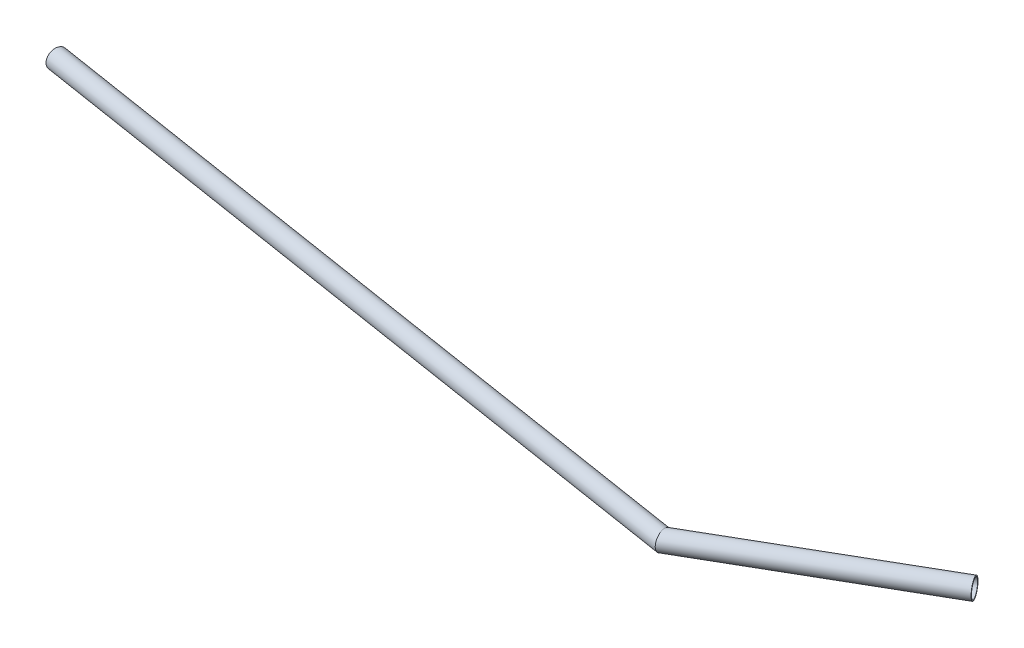
SolidWorks part; units mm, degrees
ref_plane "Front Plane" through (0, 0, 0) normal (0, 0, 1) x (1, 0, 0)
ref_plane "Top Plane" through (0, 0, 0) normal (0, 1, 0) x (1, 0, 0)
ref_plane "Right Plane" through (0, 0, 0) normal (1, 0, 0) x (0, 0, -1)
sketch "Sketch1" plane through (0, 0, 0) normal (0, 1, 0) x (1, 0, 0)
  line L0 (-465, 0) -> (465, 0) construction
  line L1 (465, 0) -> (265, -115.4701)
  line L2 (-465, 0) -> (265, -115.4701)
  point P3 (0, 0)
  dimension "D1" = 930
  dimension "D2" = 30
  dimension "D3" = 200
ref_plane "Plane1" through (-465, 0, 0) normal (0.9877, 0, 0.1562) x (0.1562, 0, -0.9877)
sketch "Sketch2" plane through (-465, 0, 0) normal (0.9877, 0, 0.1562) x (0.1562, 0, -0.9877)
  line L0 (0, 0) -> (145.2992, 0) construction
  line L1 (145.2992, 0) -> (0, 0) construction
  circle A0 centre (0, 0) radius 9.525
  dimension "D1" = 19.05
sweep "Sweep-Thin1" add profiles "Sketch2" path "Sketch1" parameters "D1"=1
sketch "Sketch3" plane through (0, 0, 0) normal (0, 1, 0) x (1, 0, 0)
  point P0 (266.8423, -125.4049)
